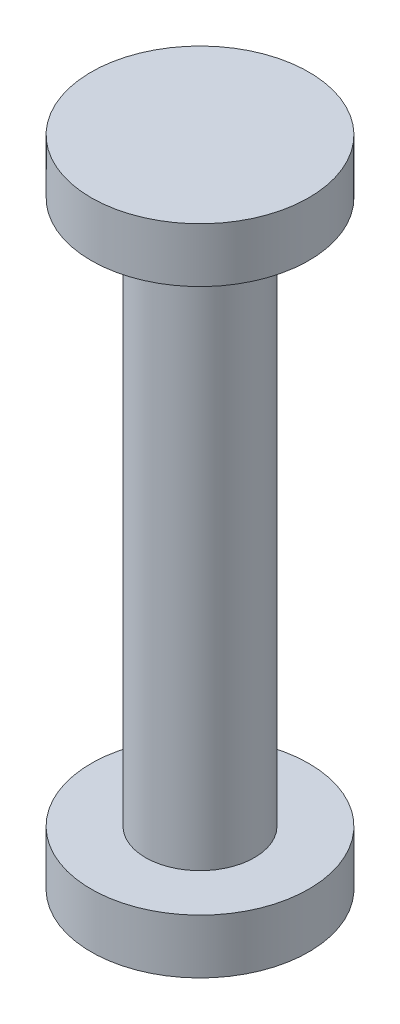
SolidWorks part; units mm, degrees
ref_plane "Front Plane" through (0, 0, 0) normal (0, 0, 1) x (1, 0, 0)
ref_plane "Top Plane" through (0, 0, 0) normal (0, 1, 0) x (1, 0, 0)
ref_plane "Right Plane" through (0, 0, 0) normal (1, 0, 0) x (0, 0, -1)
sketch "Sketch1" plane through (0, 0, 0) normal (0, 1, 0) x (1, 0, 0)
  circle A0 centre (0, 0) radius 5
  dimension "D1" = 10
extrude "Boss-Extrude2" add sketch "Sketch1" along normal blind 50
sketch "Sketch2" plane through (0, 50, 0) normal (0, 1, 0) x (1, 0, 0)
  circle A0 centre (0, 0) radius 10
  dimension "D1" = 20
extrude "Boss-Extrude3" add sketch "Sketch2" along normal blind 5
sketch "Sketch3" plane through (0, 0, 0) normal (0, -1, 0) x (-1, 0, 0)
  circle A0 centre (0, 0) radius 10
  dimension "D1" = 20
extrude "Boss-Extrude4" add sketch "Sketch3" along normal blind 5
